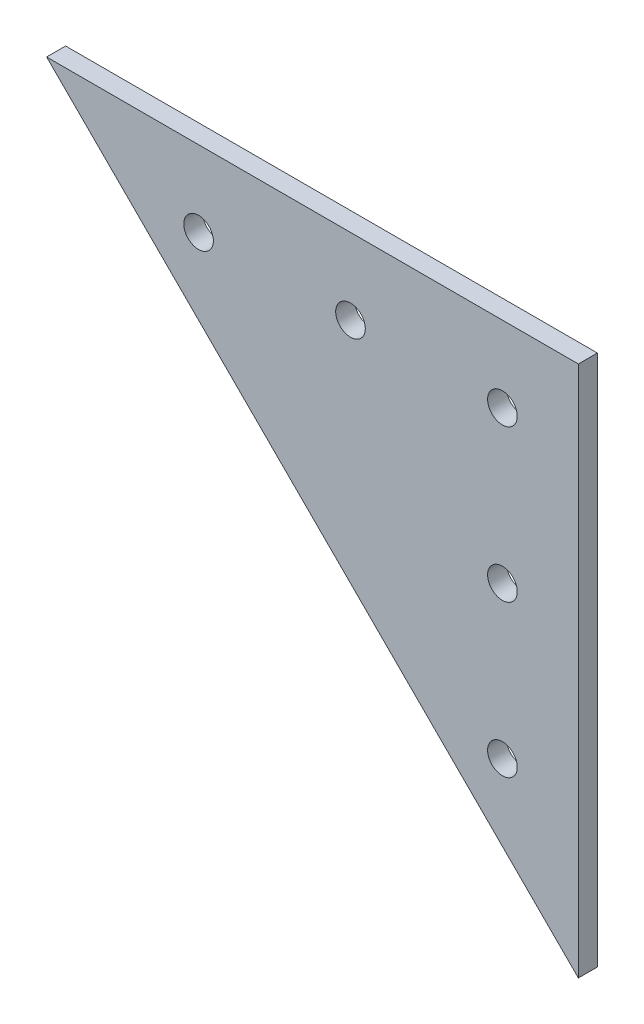
SolidWorks part; units mm, degrees
ref_plane "Front Plane" through (0, 0, 0) normal (0, 0, 1) x (1, 0, 0)
ref_plane "Top Plane" through (0, 0, 0) normal (0, 1, 0) x (1, 0, 0)
ref_plane "Right Plane" through (0, 0, 0) normal (1, 0, 0) x (0, 0, -1)
sketch "Sketch1" plane through (0, 0, 0) normal (0, 0, 1) x (1, 0, 0)
  line L1 (-44.45, 44.45) -> (44.45, 44.45)
  line L4 (44.45, 44.45) -> (44.45, -44.45)
  line L5 (-44.45, 44.45) -> (44.45, -44.45)
  line L6 (-19.05, 19.05) -> (19.05, 19.05) construction
  line L7 (19.05, 19.05) -> (19.05, -19.05) construction
  circle A0 centre (6.35, 31.75) radius 2.4765
  circle A1 centre (31.75, 31.75) radius 2.4765
  circle A2 centre (31.75, 6.35) radius 2.4765
  circle A3 centre (31.75, -19.05) radius 2.4765
  circle A4 centre (-19.05, 31.75) radius 2.4765
  point P0 (0, 0)
  point P7 (0, 44.45)
  point P9 (44.45, 0)
  dimension "D5" = 4.953
  dimension "D6" = 12.7
  dimension "D7" = 12.7
  dimension "D8" = 25.4
  dimension "D9" = 25.4
  dimension "D10" = 25.4
  dimension "D11" = 25.4
  dimension "D1" = 88.9
  dimension "D2" = 88.9
  dimension "D3" = 25.4
  dimension "D4" = 25.4
extrude "Boss-Extrude1" add sketch "Sketch1" along normal mid plane 3.175
